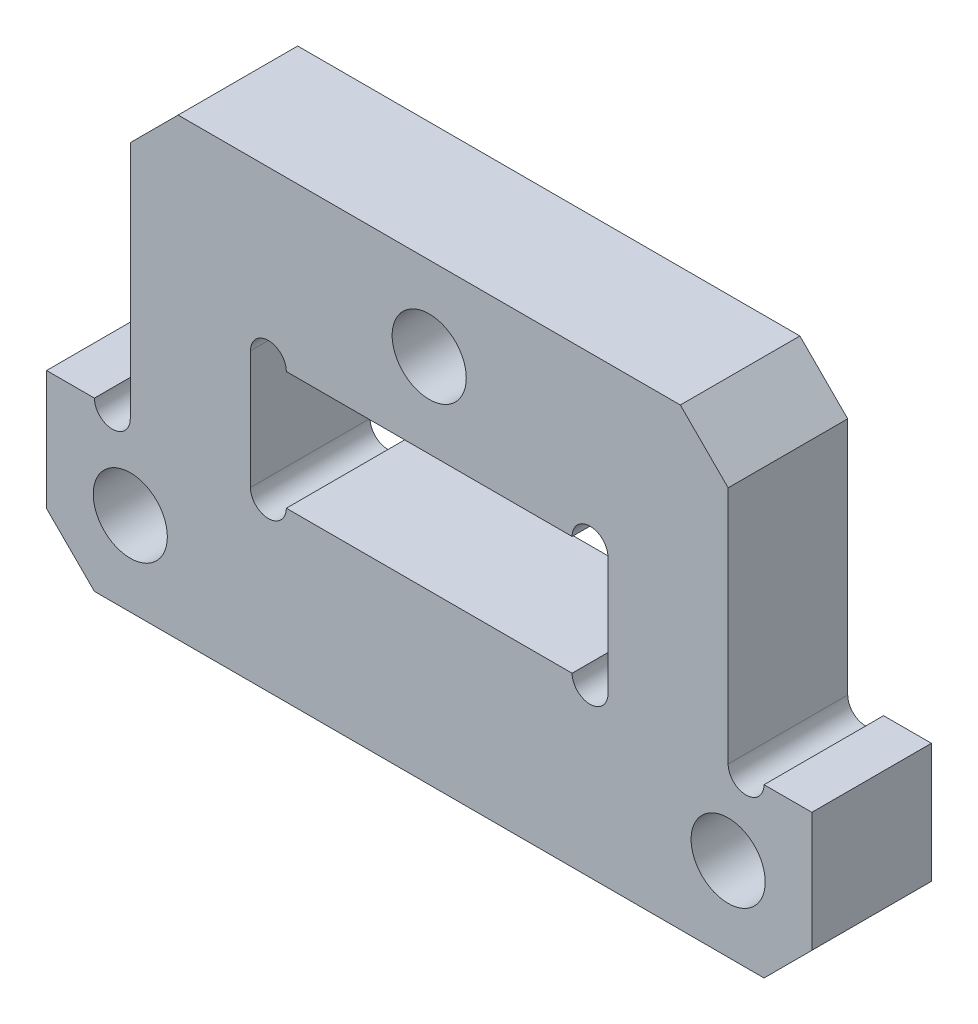
SolidWorks part; units mm, degrees
ref_plane "前视基准面" through (0, 0, 0) normal (0, 0, 1) x (1, 0, 0)
ref_plane "上视基准面" through (0, 0, 0) normal (0, 1, 0) x (1, 0, 0)
ref_plane "右视基准面" through (0, 0, 0) normal (1, 0, 0) x (0, 0, -1)
sketch "草图1" plane through (0, 0, 0) normal (0, 0, 1) x (1, 0, 0)
  line L0 (-12.5, -6) -> (12.5, -6) construction
  line L1 (7.475, -2.475) -> (-7.475, -2.475)
  line L2 (7.475, -2.475) -> (7.475, 2.475)
  line L3 (7.475, 2.475) -> (-7.475, 2.475)
  line L4 (-7.475, -2.475) -> (-7.475, 2.475)
  line L5 (7.475, -2.475) -> (-7.475, 2.475) construction
  line L6 (7.475, 2.475) -> (-7.475, -2.475) construction
  line L7 (-16, -2.5) -> (-16, -9.5)
  line L8 (-16, -9.5) -> (16, -9.5)
  line L9 (16, -9.5) -> (16, -2.5)
  line L10 (12.5, 9.5) -> (-12.5, 9.5)
  line L11 (-16, -2.5) -> (-12.5, -2.5)
  line L12 (-12.5, -2.5) -> (-12.5, 9.5)
  line L13 (16, -2.5) -> (12.5, -2.5)
  line L14 (12.5, -2.5) -> (12.5, 9.5)
  circle A0 centre (-12.5, -6) radius 1.55
  circle A1 centre (12.5, -6) radius 1.55
  circle A2 centre (0, 6) radius 1.55
  point P0 (0, 0)
  point P8 (0, -6)
  point P11 (0, 9.5)
  point P13 (0, 0)
  dimension "D4" = 3.1
  dimension "D10" = 6
  dimension "D11" = 3.5
  dimension "D1" = 4.95
  dimension "D2" = 14.95
  dimension "D3" = 6
  dimension "D5" = 25
  dimension "D6" = 3.5
  dimension "D7" = 3.5
  dimension "D8" = 2.5
  dimension "D9" = 25
extrude "凸台-拉伸1" add sketch "草图1" along normal mid plane 5
sketch "草图2" plane through (0, 0, 2.5) normal (0, 0, 1) x (1, 0, 0)
  line L0 (-12.5, -2.5) -> (-16, -2.5) construction
  line L1 (-7.475, -2.475) -> (7.475, -2.475) construction
  line L2 (7.475, 2.475) -> (-7.475, 2.475) construction
  line L3 (16, -2.5) -> (12.5, -2.5) construction
  circle A0 centre (-13.25, -2.5) radius 0.75
  circle A1 centre (-6.725, -2.475) radius 0.75
  circle A2 centre (-6.725, 2.475) radius 0.75
  circle A3 centre (6.725, 2.475) radius 0.75
  circle A4 centre (6.725, -2.475) radius 0.75
  circle A5 centre (13.25, -2.5) radius 0.75
  dimension "D1" = 1.5
extrude "切除-拉伸1" cut sketch "草图2" against normal through all
chamfer "倒角1" distance 2 angle 45 4 edges at (12.5, 9.5, 0) (-12.5, 9.5, 0) (16, -9.5, 0) (-16, -9.5, 0)
